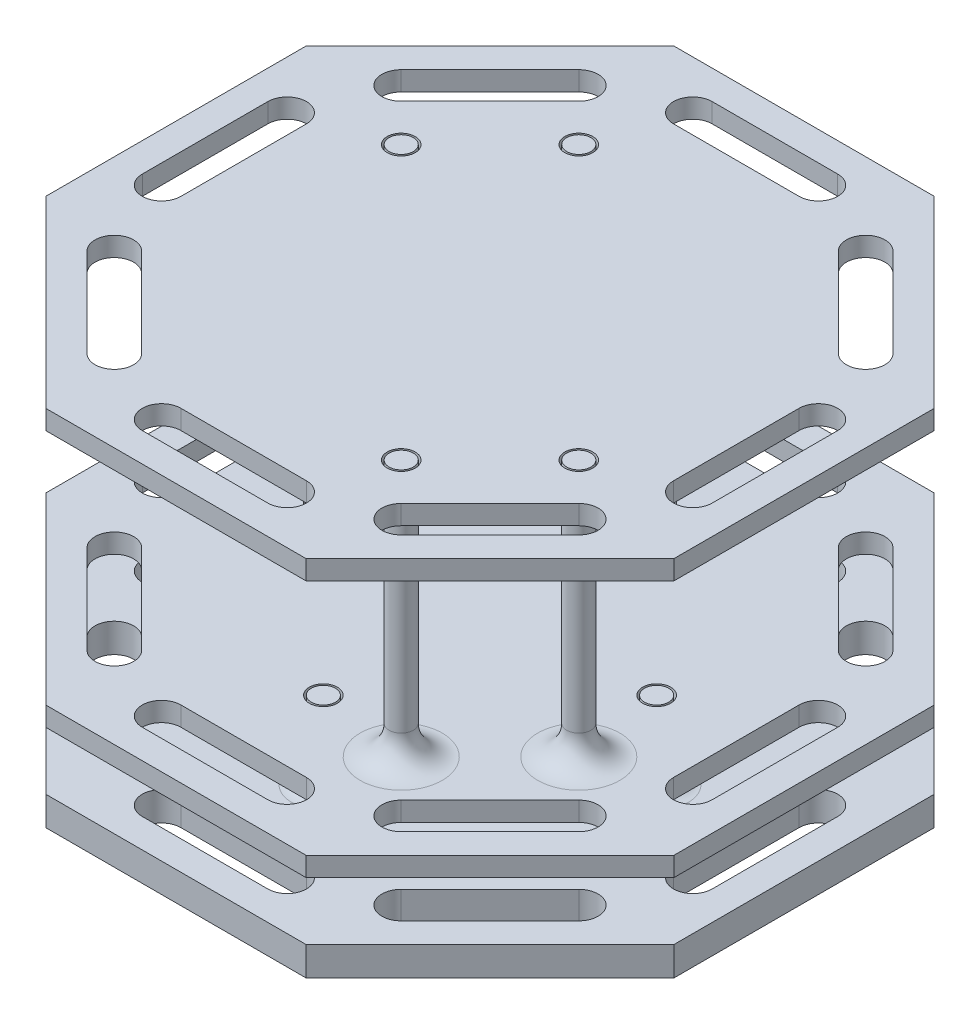
SolidWorks part; units mm, degrees
ref_plane "Front Plane" through (0, 0, 0) normal (0, 0, 1) x (1, 0, 0)
ref_plane "Top Plane" through (0, 0, 0) normal (0, 1, 0) x (1, 0, 0)
ref_plane "Right Plane" through (0, 0, 0) normal (1, 0, 0) x (0, 0, -1)
sketch "Sketch1" plane through (0, 0, 0) normal (0, 1, 0) x (1, 0, 0)
  line L0 (0, 0) -> (-17.78, 5.969) construction
  line L1 (41.275, 17.0967) -> (17.0967, 41.275)
  line L2 (17.0967, 41.275) -> (-17.0967, 41.275)
  line L3 (-17.0967, 41.275) -> (-41.275, 17.0967)
  line L4 (-41.275, 17.0967) -> (-41.275, -17.0967)
  line L5 (-41.275, -17.0967) -> (-17.0967, -41.275)
  line L6 (-17.0967, -41.275) -> (17.0967, -41.275)
  line L7 (17.0967, -41.275) -> (41.275, -17.0967)
  line L8 (41.275, -17.0967) -> (41.275, 17.0967)
  line L9 (0, 0) -> (5.969, 17.78) construction
  line L10 (-8.255, 34.925) -> (8.255, 34.925) construction
  line L11 (-8.255, 37.465) -> (8.255, 37.465)
  line L12 (-8.255, 32.385) -> (8.255, 32.385)
  line L13 (17.0625, 28.7368) -> (28.7368, 17.0625)
  line L14 (20.6546, 32.3289) -> (32.3289, 20.6546)
  line L15 (18.8585, 30.5329) -> (30.5329, 18.8585) construction
  line L16 (32.385, 8.255) -> (32.385, -8.255)
  line L17 (37.465, 8.255) -> (37.465, -8.255)
  line L18 (34.925, 8.255) -> (34.925, -8.255) construction
  line L19 (28.7368, -17.0625) -> (17.0625, -28.7368)
  line L20 (32.3289, -20.6546) -> (20.6546, -32.3289)
  line L21 (30.5329, -18.8585) -> (18.8585, -30.5329) construction
  line L22 (8.255, -32.385) -> (-8.255, -32.385)
  line L23 (8.255, -37.465) -> (-8.255, -37.465)
  line L24 (8.255, -34.925) -> (-8.255, -34.925) construction
  line L25 (-17.0625, -28.7368) -> (-28.7368, -17.0625)
  line L26 (-20.6546, -32.3289) -> (-32.3289, -20.6546)
  line L27 (-18.8585, -30.5329) -> (-30.5329, -18.8585) construction
  line L28 (-32.385, -8.255) -> (-32.385, 8.255)
  line L29 (-37.465, -8.255) -> (-37.465, 8.255)
  line L30 (-34.925, -8.255) -> (-34.925, 8.255) construction
  line L31 (-28.7368, 17.0625) -> (-17.0625, 28.7368)
  line L32 (-32.3289, 20.6546) -> (-20.6546, 32.3289)
  line L33 (-30.5329, 18.8585) -> (-18.8585, 30.5329) construction
  line L34 (0, 0) -> (8.255, 32.385) construction
  circle A0 centre (0, 0) radius 41.275 construction
  circle A1 centre (-17.78, 5.969) radius 1.5
  circle A2 centre (-17.78, -5.969) radius 1.5
  circle A3 centre (5.969, 17.78) radius 1.5
  circle A4 centre (-5.969, 17.78) radius 1.5
  circle A5 centre (17.78, -5.969) radius 1.5
  circle A6 centre (17.78, 5.969) radius 1.5
  circle A7 centre (-5.969, -17.78) radius 1.5
  circle A8 centre (5.969, -17.78) radius 1.5
  arc A9 (-8.255, 37.465) -> (-8.255, 32.385) centre (-8.255, 34.925) ccw
  arc A10 (8.255, 32.385) -> (8.255, 37.465) centre (8.255, 34.925) ccw
  arc A11 (20.6546, 32.3289) -> (17.0625, 28.7368) centre (18.8585, 30.5329) ccw
  arc A12 (28.7368, 17.0625) -> (32.3289, 20.6546) centre (30.5329, 18.8585) ccw
  arc A13 (37.465, 8.255) -> (32.385, 8.255) centre (34.925, 8.255) ccw
  arc A14 (32.385, -8.255) -> (37.465, -8.255) centre (34.925, -8.255) ccw
  arc A15 (32.3289, -20.6546) -> (28.7368, -17.0625) centre (30.5329, -18.8585) ccw
  arc A16 (17.0625, -28.7368) -> (20.6546, -32.3289) centre (18.8585, -30.5329) ccw
  arc A17 (8.255, -37.465) -> (8.255, -32.385) centre (8.255, -34.925) ccw
  arc A18 (-8.255, -32.385) -> (-8.255, -37.465) centre (-8.255, -34.925) ccw
  arc A19 (-20.6546, -32.3289) -> (-17.0625, -28.7368) centre (-18.8585, -30.5329) ccw
  arc A20 (-28.7368, -17.0625) -> (-32.3289, -20.6546) centre (-30.5329, -18.8585) ccw
  arc A21 (-37.465, -8.255) -> (-32.385, -8.255) centre (-34.925, -8.255) ccw
  arc A22 (-32.385, 8.255) -> (-37.465, 8.255) centre (-34.925, 8.255) ccw
  arc A23 (-32.3289, 20.6546) -> (-28.7368, 17.0625) centre (-30.5329, 18.8585) ccw
  arc A24 (-17.0625, 28.7368) -> (-20.6546, 32.3289) centre (-18.8585, 30.5329) ccw
  point P17 (0, 34.925)
  point P41 (24.6957, 24.6957)
  point P48 (34.925, 0)
  point P55 (24.6957, -24.6957)
  point P62 (0, -34.925)
  point P69 (-24.6957, -24.6957)
  point P76 (-34.925, 0)
  point P83 (-24.6957, 24.6957)
  dimension "D2" = 3
  dimension "D9" = 2.54
  dimension "D3" = 17.78
  dimension "D4" = 5.969
  dimension "D5" = 11.938
  dimension "D7" = 90
  dimension "D8" = 82.55
  dimension "D10" = 16.51
  dimension "D12" = 3.81
  dimension "D6" = 4
  dimension "D11" = 8
extrude "Boss-Extrude1" add sketch "Sketch1" along normal blind 3.81
sketch "Sketch2" plane through (0, 3.81, 0) normal (0, 1, 0) x (1, 0, 0)
  line L0 (0, 41.275) -> (0, -41.275) construction
  line L1 (17.0967, 41.275) -> (-17.0967, 41.275) construction
  line L2 (-17.0967, -41.275) -> (17.0967, -41.275) construction
  line L3 (-41.275, 0) -> (41.275, 0) construction
  line L4 (-41.275, 17.0967) -> (-41.275, -17.0967) construction
  line L5 (41.275, -17.0967) -> (41.275, 17.0967) construction
  line L6 (0, -21.9118) -> (21.9118, 0) construction
  line L7 (-21.9118, 0) -> (0, 21.9118) construction
  circle A4 centre (-21.9118, 0) radius 1.5875
  circle A5 centre (21.9118, 0) radius 1.5875
  circle A6 centre (0, 21.9118) radius 1.5875
  circle A7 centre (0, -21.9118) radius 1.5875
  dimension "D5" = 45
  dimension "D10" = 3.175
  dimension "D2" = 30.988
  dimension "D3" = 30.988
  dimension "D4" = 45
extrude "Boss-Extrude2" add sketch "Sketch2" along normal blind 10.16
fillet "Fillet1" radius 2.54 4 edges at (0, 3.81, 23.4993) (21.9118, 3.81, 1.5875) (0, 3.81, -20.3243) (-21.9118, 3.81, 1.5875)
sketch "Sketch3" plane through (0, 13.97, 0) normal (0, 1, 0) x (1, 0, 0)
  line L5 (-37.465, 8.255) -> (-37.465, -8.255) construction
  line L6 (-37.465, 8.255) -> (-37.465, -8.255)
  line L7 (-32.3289, -20.6546) -> (-20.6546, -32.3289) construction
  line L8 (41.275, -17.0967) -> (41.275, 17.0967)
  line L9 (41.275, 17.0967) -> (17.0967, 41.275)
  line L10 (17.0967, 41.275) -> (-17.0967, 41.275)
  line L11 (-17.0967, 41.275) -> (-41.275, 17.0967)
  line L12 (-41.275, 17.0967) -> (-41.275, -17.0967)
  line L13 (-41.275, -17.0967) -> (-17.0967, -41.275)
  line L14 (-17.0967, -41.275) -> (17.0967, -41.275)
  line L15 (17.0967, -41.275) -> (41.275, -17.0967)
  line L16 (41.275, -17.0967) -> (41.275, 17.0967)
  line L17 (41.275, 17.0967) -> (17.0967, 41.275)
  line L18 (17.0967, 41.275) -> (-17.0967, 41.275)
  line L19 (-17.0967, 41.275) -> (-41.275, 17.0967)
  line L20 (-41.275, 17.0967) -> (-41.275, -17.0967)
  line L21 (-41.275, -17.0967) -> (-17.0967, -41.275)
  line L22 (-17.0967, -41.275) -> (17.0967, -41.275)
  line L23 (17.0967, -41.275) -> (41.275, -17.0967)
  line L24 (-17.0625, -28.7368) -> (-28.7368, -17.0625) construction
  line L25 (-8.255, -37.465) -> (8.255, -37.465) construction
  line L26 (8.255, -32.385) -> (-8.255, -32.385) construction
  line L27 (20.6546, -32.3289) -> (32.3289, -20.6546) construction
  line L28 (28.7368, -17.0625) -> (17.0625, -28.7368) construction
  line L29 (37.465, -8.255) -> (37.465, 8.255) construction
  line L30 (32.385, 8.255) -> (32.385, -8.255) construction
  line L31 (17.0625, 28.7368) -> (28.7368, 17.0625) construction
  line L32 (32.3289, 20.6546) -> (20.6546, 32.3289) construction
  line L33 (-8.255, 32.385) -> (8.255, 32.385) construction
  line L34 (8.255, 37.465) -> (-8.255, 37.465) construction
  line L35 (-20.6546, 32.3289) -> (-32.3289, 20.6546) construction
  line L36 (-28.7368, 17.0625) -> (-17.0625, 28.7368) construction
  line L37 (-32.385, -8.255) -> (-32.385, 8.255) construction
  line L38 (-32.3289, -20.6546) -> (-20.6546, -32.3289)
  line L39 (-17.0625, -28.7368) -> (-28.7368, -17.0625)
  line L40 (-8.255, -37.465) -> (8.255, -37.465)
  line L41 (8.255, -32.385) -> (-8.255, -32.385)
  line L42 (20.6546, -32.3289) -> (32.3289, -20.6546)
  line L43 (28.7368, -17.0625) -> (17.0625, -28.7368)
  line L44 (37.465, -8.255) -> (37.465, 8.255)
  line L45 (32.385, 8.255) -> (32.385, -8.255)
  line L46 (17.0625, 28.7368) -> (28.7368, 17.0625)
  line L47 (32.3289, 20.6546) -> (20.6546, 32.3289)
  line L48 (-8.255, 32.385) -> (8.255, 32.385)
  line L49 (8.255, 37.465) -> (-8.255, 37.465)
  line L50 (-20.6546, 32.3289) -> (-32.3289, 20.6546)
  line L51 (-28.7368, 17.0625) -> (-17.0625, 28.7368)
  line L52 (-32.385, -8.255) -> (-32.385, 8.255)
  arc A5 (-37.465, -8.255) -> (-32.385, -8.255) centre (-34.925, -8.255) ccw construction
  arc A6 (-37.465, -8.255) -> (-32.385, -8.255) centre (-34.925, -8.255) ccw
  circle A7 centre (0, -21.9118) radius 1.5875 construction
  circle A8 centre (21.9118, 0) radius 1.5875 construction
  circle A9 centre (0, 21.9118) radius 1.5875 construction
  circle A10 centre (-21.9118, 0) radius 1.5875 construction
  arc A11 (-28.7368, -17.0625) -> (-32.3289, -20.6546) centre (-30.5329, -18.8585) ccw construction
  arc A12 (-20.6546, -32.3289) -> (-17.0625, -28.7368) centre (-18.8585, -30.5329) ccw construction
  arc A13 (-8.255, -32.385) -> (-8.255, -37.465) centre (-8.255, -34.925) ccw construction
  arc A14 (8.255, -37.465) -> (8.255, -32.385) centre (8.255, -34.925) ccw construction
  arc A15 (17.0625, -28.7368) -> (20.6546, -32.3289) centre (18.8585, -30.5329) ccw construction
  arc A16 (32.3289, -20.6546) -> (28.7368, -17.0625) centre (30.5329, -18.8585) ccw construction
  arc A17 (32.385, -8.255) -> (37.465, -8.255) centre (34.925, -8.255) ccw construction
  arc A18 (37.465, 8.255) -> (32.385, 8.255) centre (34.925, 8.255) ccw construction
  arc A19 (28.7368, 17.0625) -> (32.3289, 20.6546) centre (30.5329, 18.8585) ccw construction
  arc A20 (20.6546, 32.3289) -> (17.0625, 28.7368) centre (18.8585, 30.5329) ccw construction
  arc A21 (8.255, 32.385) -> (8.255, 37.465) centre (8.255, 34.925) ccw construction
  arc A22 (-8.255, 37.465) -> (-8.255, 32.385) centre (-8.255, 34.925) ccw construction
  arc A23 (-17.0625, 28.7368) -> (-20.6546, 32.3289) centre (-18.8585, 30.5329) ccw construction
  arc A24 (-32.3289, 20.6546) -> (-28.7368, 17.0625) centre (-30.5329, 18.8585) ccw construction
  arc A25 (-32.385, 8.255) -> (-37.465, 8.255) centre (-34.925, 8.255) ccw construction
  circle A26 centre (0, -21.9118) radius 1.5875
  circle A27 centre (21.9118, 0) radius 1.5875
  circle A28 centre (0, 21.9118) radius 1.5875
  circle A29 centre (-21.9118, 0) radius 1.5875
  arc A30 (-28.7368, -17.0625) -> (-32.3289, -20.6546) centre (-30.5329, -18.8585) ccw
  arc A31 (-20.6546, -32.3289) -> (-17.0625, -28.7368) centre (-18.8585, -30.5329) ccw
  arc A32 (-8.255, -32.385) -> (-8.255, -37.465) centre (-8.255, -34.925) ccw
  arc A33 (8.255, -37.465) -> (8.255, -32.385) centre (8.255, -34.925) ccw
  arc A34 (17.0625, -28.7368) -> (20.6546, -32.3289) centre (18.8585, -30.5329) ccw
  arc A35 (32.3289, -20.6546) -> (28.7368, -17.0625) centre (30.5329, -18.8585) ccw
  arc A36 (32.385, -8.255) -> (37.465, -8.255) centre (34.925, -8.255) ccw
  arc A37 (37.465, 8.255) -> (32.385, 8.255) centre (34.925, 8.255) ccw
  arc A38 (28.7368, 17.0625) -> (32.3289, 20.6546) centre (30.5329, 18.8585) ccw
  arc A39 (20.6546, 32.3289) -> (17.0625, 28.7368) centre (18.8585, 30.5329) ccw
  arc A40 (8.255, 32.385) -> (8.255, 37.465) centre (8.255, 34.925) ccw
  arc A41 (-8.255, 37.465) -> (-8.255, 32.385) centre (-8.255, 34.925) ccw
  arc A42 (-17.0625, 28.7368) -> (-20.6546, 32.3289) centre (-18.8585, 30.5329) ccw
  arc A43 (-32.3289, 20.6546) -> (-28.7368, 17.0625) centre (-30.5329, 18.8585) ccw
  arc A44 (-32.385, 8.255) -> (-37.465, 8.255) centre (-34.925, 8.255) ccw
  circle A45 centre (0, 21.9118) radius 1.8415
  circle A46 centre (-21.9118, 0) radius 1.8415
  circle A47 centre (0, -21.9118) radius 1.8415
  circle A48 centre (21.9118, 0) radius 1.8415
  dimension "D1" = 0
  dimension "D2" = 0.254
extrude "Boss-Extrude3" add sketch "Sketch3" against normal blind 2.54 separate body contours L22 L23 L16 L17 L18 L19 L20 L21 A48 A47 A46 A45 A44 L52 A6 L6 A43 L50 A42 L51 A41 L49 A40 L48 A39 L47 A38 L46 A37 L44 A36 L45 A35 L42 A34 L43 A33 L40 A32 L41
sketch "Sketch4" plane through (0, 13.97, 0) normal (0, 1, 0) x (1, 0, 0)
  line L0 (-29.1858, -29.1858) -> (29.1858, 29.1858) construction
  line L1 (-41.275, -17.0967) -> (-17.0967, -41.275) construction
  line L2 (41.275, 17.0967) -> (17.0967, 41.275) construction
  line L3 (-23.7977, 12.1233) -> (-12.1233, 23.7977) construction
  line L4 (-17.9605, 17.9605) -> (0, 0) construction
  circle A0 centre (-23.7977, 12.1233) radius 1.5875
  circle A1 centre (-12.1233, 23.7977) radius 1.5875
  circle A2 centre (23.7977, -12.1233) radius 1.5875
  circle A3 centre (12.1233, -23.7977) radius 1.5875
  dimension "D1" = 25.4
  dimension "D2" = 3.175
  dimension "D3" = 16.51
extrude "Boss-Extrude4" add sketch "Sketch4" along normal blind 33.782
fillet "Fillet2" radius 3.81 4 edges at (23.7977, 13.97, 10.5358) (12.1233, 13.97, 22.2102) (-12.1233, 13.97, -22.2102) (-23.7977, 13.97, -10.5358)
sketch "Sketch5" plane through (0, 47.752, 0) normal (0, 1, 0) x (1, 0, 0)
  line L0 (-28.7368, 17.0625) -> (-17.0625, 28.7368) construction
  line L1 (-20.6546, 32.3289) -> (-32.3289, 20.6546) construction
  line L2 (-37.465, 8.255) -> (-37.465, -8.255) construction
  line L3 (-32.385, -8.255) -> (-32.385, 8.255) construction
  line L4 (-17.0625, -28.7368) -> (-28.7368, -17.0625) construction
  line L5 (-32.3289, -20.6546) -> (-20.6546, -32.3289) construction
  line L6 (-8.255, -37.465) -> (8.255, -37.465) construction
  line L7 (8.255, -32.385) -> (-8.255, -32.385) construction
  line L8 (-17.0967, -41.275) -> (17.0967, -41.275)
  line L9 (17.0967, -41.275) -> (41.275, -17.0967)
  line L10 (41.275, -17.0967) -> (41.275, 17.0967)
  line L11 (41.275, 17.0967) -> (17.0967, 41.275)
  line L12 (17.0967, 41.275) -> (-17.0967, 41.275)
  line L13 (-17.0967, 41.275) -> (-41.275, 17.0967)
  line L14 (-41.275, 17.0967) -> (-41.275, -17.0967)
  line L15 (-41.275, -17.0967) -> (-17.0967, -41.275)
  line L16 (-17.0967, -41.275) -> (17.0967, -41.275)
  line L17 (17.0967, -41.275) -> (41.275, -17.0967)
  line L18 (41.275, -17.0967) -> (41.275, 17.0967)
  line L19 (41.275, 17.0967) -> (17.0967, 41.275)
  line L20 (17.0967, 41.275) -> (-17.0967, 41.275)
  line L21 (-17.0967, 41.275) -> (-41.275, 17.0967)
  line L22 (-41.275, 17.0967) -> (-41.275, -17.0967)
  line L23 (-41.275, -17.0967) -> (-17.0967, -41.275)
  line L24 (20.6546, -32.3289) -> (32.3289, -20.6546) construction
  line L25 (28.7368, -17.0625) -> (17.0625, -28.7368) construction
  line L26 (37.465, -8.255) -> (37.465, 8.255) construction
  line L27 (32.385, 8.255) -> (32.385, -8.255) construction
  line L28 (17.0625, 28.7368) -> (28.7368, 17.0625) construction
  line L29 (32.3289, 20.6546) -> (20.6546, 32.3289) construction
  line L30 (-8.255, 32.385) -> (8.255, 32.385) construction
  line L31 (8.255, 37.465) -> (-8.255, 37.465) construction
  line L32 (-28.7368, 17.0625) -> (-17.0625, 28.7368)
  line L33 (-20.6546, 32.3289) -> (-32.3289, 20.6546)
  line L34 (-37.465, 8.255) -> (-37.465, -8.255)
  line L35 (-32.385, -8.255) -> (-32.385, 8.255)
  line L36 (-17.0625, -28.7368) -> (-28.7368, -17.0625)
  line L37 (-32.3289, -20.6546) -> (-20.6546, -32.3289)
  line L38 (-8.255, -37.465) -> (8.255, -37.465)
  line L39 (8.255, -32.385) -> (-8.255, -32.385)
  line L40 (20.6546, -32.3289) -> (32.3289, -20.6546)
  line L41 (28.7368, -17.0625) -> (17.0625, -28.7368)
  line L42 (37.465, -8.255) -> (37.465, 8.255)
  line L43 (32.385, 8.255) -> (32.385, -8.255)
  line L44 (17.0625, 28.7368) -> (28.7368, 17.0625)
  line L45 (32.3289, 20.6546) -> (20.6546, 32.3289)
  line L46 (-8.255, 32.385) -> (8.255, 32.385)
  line L47 (8.255, 37.465) -> (-8.255, 37.465)
  circle A0 centre (12.1233, -23.7977) radius 1.5875 construction
  circle A1 centre (23.7977, -12.1233) radius 1.5875 construction
  circle A2 centre (-23.7977, 12.1233) radius 1.5875 construction
  circle A3 centre (-12.1233, 23.7977) radius 1.5875 construction
  arc A4 (-17.0625, 28.7368) -> (-20.6546, 32.3289) centre (-18.8585, 30.5329) ccw construction
  arc A5 (-32.3289, 20.6546) -> (-28.7368, 17.0625) centre (-30.5329, 18.8585) ccw construction
  arc A6 (-32.385, 8.255) -> (-37.465, 8.255) centre (-34.925, 8.255) ccw construction
  arc A7 (-37.465, -8.255) -> (-32.385, -8.255) centre (-34.925, -8.255) ccw construction
  arc A8 (-28.7368, -17.0625) -> (-32.3289, -20.6546) centre (-30.5329, -18.8585) ccw construction
  arc A9 (-20.6546, -32.3289) -> (-17.0625, -28.7368) centre (-18.8585, -30.5329) ccw construction
  arc A10 (-8.255, -32.385) -> (-8.255, -37.465) centre (-8.255, -34.925) ccw construction
  arc A11 (8.255, -37.465) -> (8.255, -32.385) centre (8.255, -34.925) ccw construction
  arc A12 (17.0625, -28.7368) -> (20.6546, -32.3289) centre (18.8585, -30.5329) ccw construction
  arc A13 (32.3289, -20.6546) -> (28.7368, -17.0625) centre (30.5329, -18.8585) ccw construction
  arc A14 (32.385, -8.255) -> (37.465, -8.255) centre (34.925, -8.255) ccw construction
  arc A15 (37.465, 8.255) -> (32.385, 8.255) centre (34.925, 8.255) ccw construction
  arc A16 (28.7368, 17.0625) -> (32.3289, 20.6546) centre (30.5329, 18.8585) ccw construction
  arc A17 (20.6546, 32.3289) -> (17.0625, 28.7368) centre (18.8585, 30.5329) ccw construction
  arc A18 (8.255, 32.385) -> (8.255, 37.465) centre (8.255, 34.925) ccw construction
  arc A19 (-8.255, 37.465) -> (-8.255, 32.385) centre (-8.255, 34.925) ccw construction
  circle A20 centre (12.1233, -23.7977) radius 1.5875
  circle A21 centre (23.7977, -12.1233) radius 1.5875
  circle A22 centre (-23.7977, 12.1233) radius 1.5875
  circle A23 centre (-12.1233, 23.7977) radius 1.5875
  arc A24 (-17.0625, 28.7368) -> (-20.6546, 32.3289) centre (-18.8585, 30.5329) ccw
  arc A25 (-32.3289, 20.6546) -> (-28.7368, 17.0625) centre (-30.5329, 18.8585) ccw
  arc A26 (-32.385, 8.255) -> (-37.465, 8.255) centre (-34.925, 8.255) ccw
  arc A27 (-37.465, -8.255) -> (-32.385, -8.255) centre (-34.925, -8.255) ccw
  arc A28 (-28.7368, -17.0625) -> (-32.3289, -20.6546) centre (-30.5329, -18.8585) ccw
  arc A29 (-20.6546, -32.3289) -> (-17.0625, -28.7368) centre (-18.8585, -30.5329) ccw
  arc A30 (-8.255, -32.385) -> (-8.255, -37.465) centre (-8.255, -34.925) ccw
  arc A31 (8.255, -37.465) -> (8.255, -32.385) centre (8.255, -34.925) ccw
  arc A32 (17.0625, -28.7368) -> (20.6546, -32.3289) centre (18.8585, -30.5329) ccw
  arc A33 (32.3289, -20.6546) -> (28.7368, -17.0625) centre (30.5329, -18.8585) ccw
  arc A34 (32.385, -8.255) -> (37.465, -8.255) centre (34.925, -8.255) ccw
  arc A35 (37.465, 8.255) -> (32.385, 8.255) centre (34.925, 8.255) ccw
  arc A36 (28.7368, 17.0625) -> (32.3289, 20.6546) centre (30.5329, 18.8585) ccw
  arc A37 (20.6546, 32.3289) -> (17.0625, 28.7368) centre (18.8585, 30.5329) ccw
  arc A38 (8.255, 32.385) -> (8.255, 37.465) centre (8.255, 34.925) ccw
  arc A39 (-8.255, 37.465) -> (-8.255, 32.385) centre (-8.255, 34.925) ccw
  circle A40 centre (-12.1233, 23.7977) radius 1.8415
  circle A41 centre (-23.7977, 12.1233) radius 1.8415
  circle A42 centre (23.7977, -12.1233) radius 1.8415
  circle A43 centre (12.1233, -23.7977) radius 1.8415
  dimension "D1" = 0
  dimension "D2" = 0.254
extrude "Boss-Extrude5" add sketch "Sketch5" against normal blind 2.54 contours L22 L23 L16 L17 L18 L19 L20 L21 A43 A42 A41 A40 A39 L47 A38 L46 A37 L45 A36 L44 A35 L42 A34 L43 A33 L40 A32 L41 A31 L38 A30 L39 A29 L37 A28 L36 A27 L34 A26 L35
